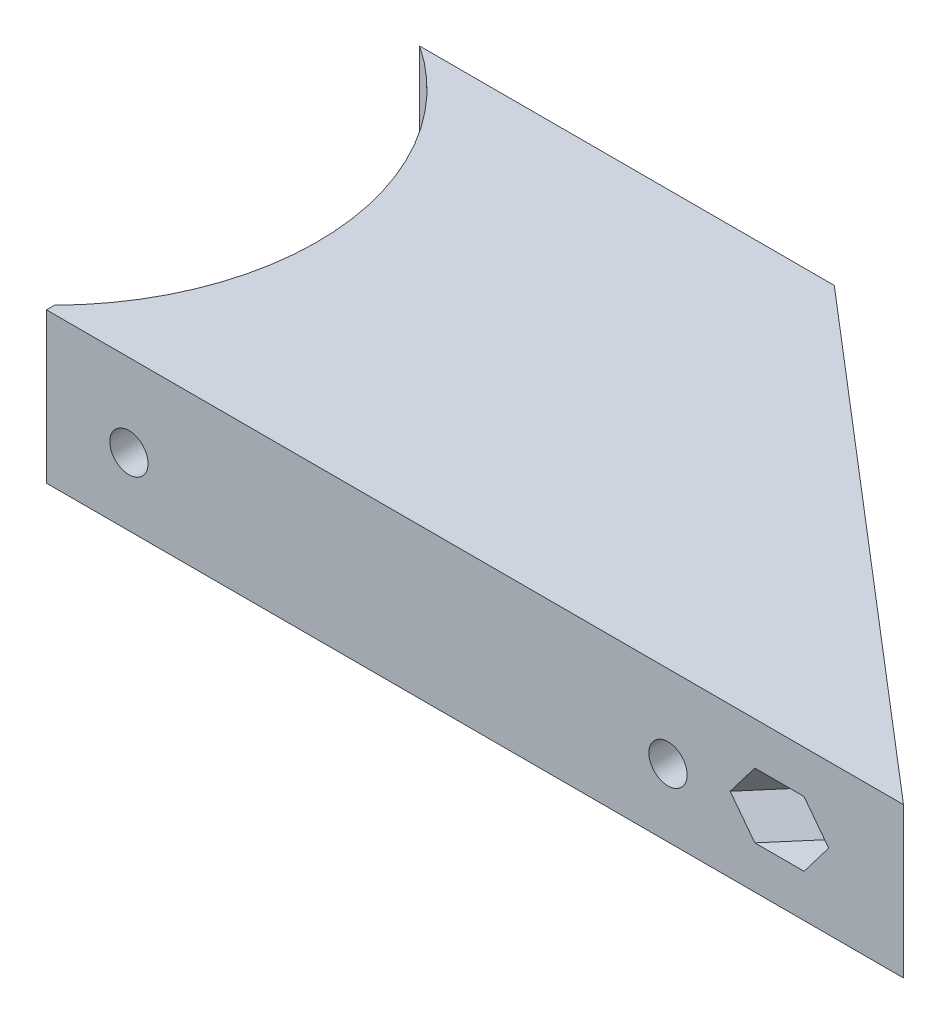
SolidWorks part; units mm, degrees
ref_plane "Alzado" through (0, 0, 0) normal (0, 0, 1) x (1, 0, 0)
ref_plane "Planta" through (0, 0, 0) normal (0, 1, 0) x (1, 0, 0)
ref_plane "Vista lateral" through (0, 0, 0) normal (1, 0, 0) x (0, 0, -1)
sketch "Croquis1" plane through (0, 0, 0) normal (0, 1, 0) x (1, 0, 0)
  line L0 (0, 0) -> (72.7832, 0)
  line L1 (72.7832, 0) -> (38.2245, 29.6204)
  line L2 (38.2245, 29.6204) -> (35.6214, 26.5833)
  line L3 (35.6214, 26.5833) -> (60.8031, 5)
  line L4 (60.8031, 5) -> (0, 5)
  line L5 (0, 5) -> (0, 0)
  dimension "D1" = 4
  dimension "D2" = 5
  dimension "D3" = 40.6
  dimension "D4" = 72.7832
extrude "Saliente-Extruir1" add sketch "Croquis1" along normal blind 12.75
sketch "Croquis2" plane through (0, 0, 0) normal (0, 0, 1) x (1, 0, 0)
  line L2 (0, 12.75) -> (72.7832, 12.75) construction
  line L3 (72.7832, 12.75) -> (72.7832, 0) construction
  circle A0 centre (52.7832, 5.75) radius 1.625
  circle A1 centre (7, 5.75) radius 1.625
  dimension "D1" = 3.25
  dimension "D2" = 20
  dimension "D3" = 7
  dimension "D4" = 45.7832
  dimension "D5" = 7
extrude "Cortar-Extruir1" cut sketch "Croquis2" against normal up to next
sketch "Croquis3" plane through (0, 12.75, 0) normal (0, 1, 0) x (1, 0, 0)
  line L0 (0, 5) -> (0, 0) construction
  line L1 (0, 0) -> (72.7832, 0) construction
  circle A0 centre (-16, 16.5) radius 22.5
  dimension "D1" = 45
  dimension "D2" = 16
  dimension "D3" = 16.5
extrude "Cortar-Extruir2" cut sketch "Croquis3" against normal through all
sketch "Croquis4" plane through (0, 12.75, 0) normal (0, 1, 0) x (1, 0, 0)
  line L0 (38.2245, 29.6204) -> (31.6563, 35.25)
  line L1 (31.6563, 35.25) -> (-3.5627, 35.25)
  line L2 (0, 0) -> (72.7832, 0) construction
  line L3 (72.7832, 0) -> (38.2245, 29.6204) construction
  line L4 (38.2245, 29.6204) -> (35.6214, 26.5833)
  line L5 (35.6214, 26.5833) -> (60.8031, 5)
  line L6 (60.8031, 5) -> (3.3391, 5)
  arc A0 (3.3391, 5) -> (-3.5627, 35.25) centre (-16, 16.5) ccw
  arc A1 (0, 0.6807) -> (3.3391, 5) centre (-16, 16.5) ccw construction
  dimension "D1" = 35.25
extrude "Saliente-Extruir2" add sketch "Croquis4" against normal blind 3
sketch "Croquis5" plane through (0, 9.75, 0) normal (0, -1, 0) x (1, 0, 0)
  line L0 (-3.5627, -35.25) -> (31.6563, -35.25)
  line L1 (31.6563, -35.25) -> (38.2245, -29.6204)
  line L2 (38.2245, -29.6204) -> (35.6214, -26.5833)
  line L3 (35.6214, -26.5833) -> (30.1767, -31.25)
  line L4 (30.1767, -31.25) -> (0.9908, -31.25)
  arc A0 (-3.5627, -35.25) -> (3.3391, -5) centre (-16, -16.5) ccw construction
  arc A1 (-3.5627, -35.25) -> (0.9908, -31.25) centre (-16, -16.5) ccw
  point P16 (0, 0)
  dimension "D1" = 4
extrude "Saliente-Extruir3" add sketch "Croquis5" along normal up to vertex (9.75 mm away) up to point (38.2244, 0, -29.6204)
sketch "Croquis6" plane through (30.8242, 0, -35.9632) normal (0.6508, 0, -0.7593) x (-0.7593, 0, -0.6508)
  line L0 (-55.2622, 12.75) -> (-55.2622, 0) construction
  line L1 (-1.0959, 0) -> (-1.0959, 12.75) construction
  circle A0 centre (-47.2622, 6.375) radius 1.625
  circle A1 centre (-16.0959, 6.375) radius 1.625
  dimension "D1" = 3.25
  dimension "D2" = 3.25
  dimension "D3" = 8
  dimension "D4" = 15
extrude "Cortar-Extruir3" cut sketch "Croquis6" against normal blind 10
sketch "Croquis7" plane through (28.2211, 0, -32.9261) normal (-0.6508, 0, 0.7593) x (0.7593, 0, 0.6508)
  line L1 (48.8499, 3.625) -> (50.4376, 6.375)
  line L2 (50.4376, 6.375) -> (48.8499, 9.125)
  line L3 (48.8499, 9.125) -> (45.6745, 9.125)
  line L4 (45.6745, 9.125) -> (44.0868, 6.375)
  line L5 (44.0868, 6.375) -> (45.6745, 3.625)
  line L6 (45.6745, 3.625) -> (48.8499, 3.625)
  circle A0 centre (47.2622, 6.375) radius 2.75 construction
  dimension "D1" = 5.5
extrude "Cortar-Extruir4" cut sketch "Croquis7" along normal blind 10 from offset 2 offset against normal yes
sketch "Croquis8" plane through (28.2211, 0, -32.9261) normal (-0.6508, 0, 0.7593) x (0.7593, 0, 0.6508)
  line L0 (45.6745, 3.625) -> (48.8499, 3.625) construction
  line L1 (17.6837, 3.625) -> (19.2714, 6.375)
  line L2 (19.2714, 6.375) -> (17.6837, 9.125)
  line L3 (17.6837, 9.125) -> (14.5082, 9.125)
  line L4 (14.5082, 9.125) -> (12.9205, 6.375)
  line L5 (12.9205, 6.375) -> (14.5082, 3.625)
  line L6 (14.5082, 3.625) -> (17.6837, 3.625)
  circle A0 centre (16.0959, 6.375) radius 2.75 construction
extrude "Cortar-Extruir5" cut sketch "Croquis8" along normal blind 10 from offset 2 offset against normal yes
sketch "Croquis9" plane through (0, 0, -5) normal (0, 0, -1) x (-1, 0, 0)
  line L1 (-5.4123, 3) -> (-3.8246, 5.75)
  line L2 (-3.8246, 5.75) -> (-5.4123, 8.5)
  line L3 (-5.4123, 8.5) -> (-8.5877, 8.5)
  line L4 (-8.5877, 8.5) -> (-10.1754, 5.75)
  line L5 (-10.1754, 5.75) -> (-8.5877, 3)
  line L6 (-8.5877, 3) -> (-5.4123, 3)
  line L7 (-51.1955, 3) -> (-49.6078, 5.75)
  line L8 (-49.6078, 5.75) -> (-51.1955, 8.5)
  line L9 (-51.1955, 8.5) -> (-54.3709, 8.5)
  line L10 (-54.3709, 8.5) -> (-55.9586, 5.75)
  line L11 (-55.9586, 5.75) -> (-54.3709, 3)
  line L12 (-54.3709, 3) -> (-51.1955, 3)
  circle A0 centre (-7, 5.75) radius 2.75 construction
  circle A1 centre (-52.7832, 5.75) radius 2.75 construction
  dimension "D1" = 5.5
extrude "Cortar-Extruir6" cut sketch "Croquis9" against normal blind 2
sketch "Croquis10" plane through (0, 0, -35.25) normal (0, 0, -1) x (-1, 0, 0)
  line L0 (-31.6563, 0) -> (-31.6563, 12.75) construction
  circle A0 centre (-21.6563, 6.375) radius 1.625
  dimension "D1" = 3.25
  dimension "D2" = 10
extrude "Cortar-Extruir7" cut sketch "Croquis10" against normal up to next
sketch "Croquis11" plane through (0, 0, -31.25) normal (0, 0, 1) x (1, 0, 0)
  line L1 (23.244, 3.625) -> (24.8317, 6.375)
  line L2 (24.8317, 6.375) -> (23.244, 9.125)
  line L3 (23.244, 9.125) -> (20.0686, 9.125)
  line L4 (20.0686, 9.125) -> (18.4809, 6.375)
  line L5 (18.4809, 6.375) -> (20.0686, 3.625)
  line L6 (20.0686, 3.625) -> (23.244, 3.625)
  circle A0 centre (21.6563, 6.375) radius 2.75 construction
  dimension "D1" = 5.5
extrude "Cortar-Extruir8" cut sketch "Croquis11" against normal blind 2
